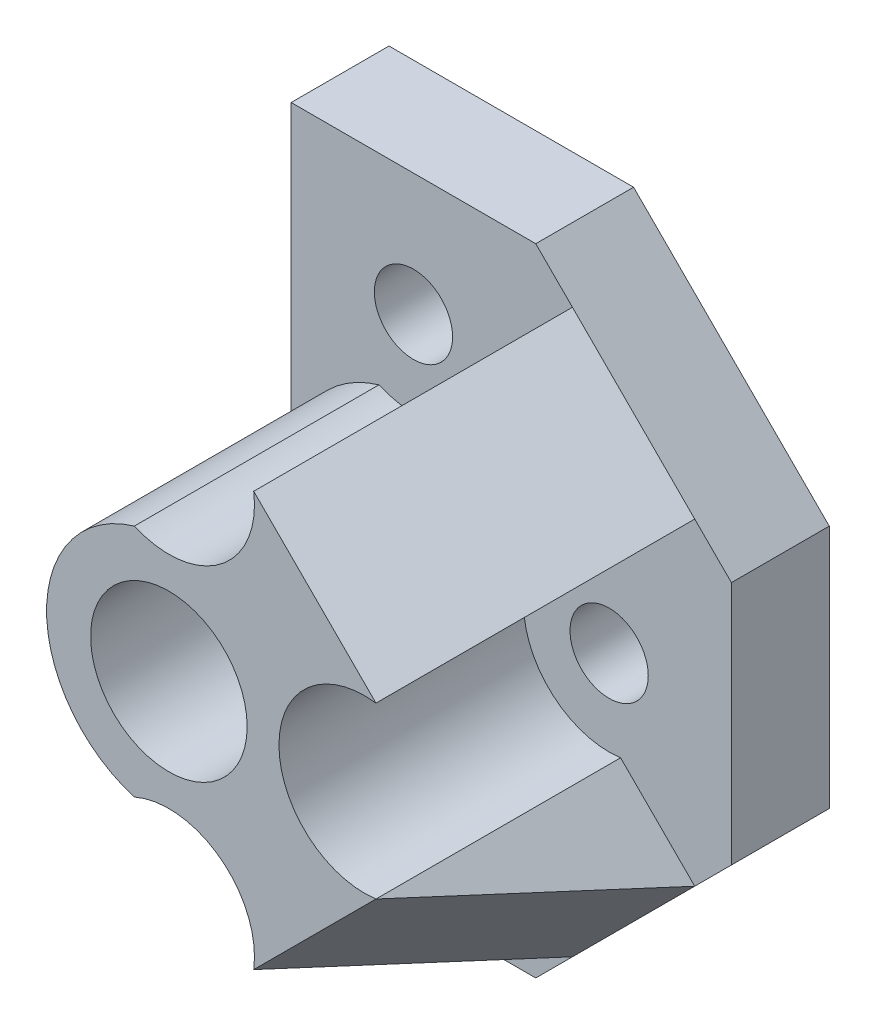
SolidWorks part; units mm, degrees
ref_plane "前视基准面" through (0, 0, 0) normal (0, 0, 1) x (1, 0, 0)
ref_plane "上视基准面" through (0, 0, 0) normal (0, 1, 0) x (1, 0, 0)
ref_plane "右视基准面" through (0, 0, 0) normal (1, 0, 0) x (0, 0, -1)
sketch "草图1" plane through (0, 0, 0) normal (0, 0, 1) x (1, 0, 0)
  line L0 (0, 0) -> (0, 26)
  line L1 (0, 26) -> (10, 26)
  line L2 (18, 18) -> (10, 26)
  line L3 (10, 0) -> (18, 8)
  line L4 (18, 18) -> (18, 8)
  line L7 (10, 0) -> (0, 0)
  circle A0 centre (5, 21) radius 1.6
  circle A1 centre (5, 13) radius 3.2
  circle A2 centre (5, 5) radius 1.6
  circle A3 centre (13, 13) radius 1.6
extrude "凸台-拉伸1" add sketch "草图1" along normal blind 4
sketch "草图2" plane through (0, 0, 4) normal (0, 0, 1) x (1, 0, 0)
  line L1 (13.4685, 16.4685) -> (16.5, 19.5)
  line L2 (18, 18) -> (10, 26) construction
  line L3 (16.5, 19.5) -> (11.5, 24.5)
  line L4 (11.5, 24.5) -> (8.4685, 21.4685)
  line L5 (8.4685, 4.5315) -> (11.5, 1.5)
  line L6 (10, 0) -> (18, 8) construction
  line L7 (11.5, 1.5) -> (16.5, 6.5)
  line L8 (16.5, 6.5) -> (13.4685, 9.5315)
  circle A0 centre (5, 13) radius 3.2
  arc A1 (3.5893, 17.7969) -> (3.5893, 8.2031) centre (5, 13) ccw
  arc A5 (8.4685, 4.5315) -> (3.5893, 8.2031) centre (5, 5) ccw
  arc A6 (13.4685, 16.4685) -> (13.4685, 9.5315) centre (13, 13) ccw
  arc A7 (3.5893, 17.7969) -> (8.4685, 21.4685) centre (5, 21) ccw
extrude "凸台-拉伸2" add sketch "草图2" along normal blind 10
sketch "草图3" plane through (-1.5, 1.5, 0) normal (0.7071, -0.7071, 0) x (0, 0, -1)
  line L0 (-4, 25.4558) -> (-14, 25.4558)
  line L1 (-14, 25.4558) -> (-14, 21.1687)
  line L2 (-14, 21.1687) -> (-4, 25.4558)
  line L3 (-14, 21.1687) -> (-4, 21.1687) construction
  line L4 (-14, 21.1687) -> (-14, 25.4558) construction
extrude "切除-拉伸1" cut sketch "草图3" against normal blind 10
sketch "草图4" plane through (11.5, 11.5, 0) normal (0.7071, 0.7071, 0) x (0, 0, -1)
  line L0 (-4, -7.0711) -> (-14, -2.7839)
  line L1 (-14, -2.7839) -> (-14, -7.0711)
  line L2 (-14, -7.0711) -> (-4, -7.0711)
  line L3 (-14, -2.7839) -> (-4, -2.7839) construction
extrude "切除-拉伸2" cut sketch "草图4" against normal blind 10
